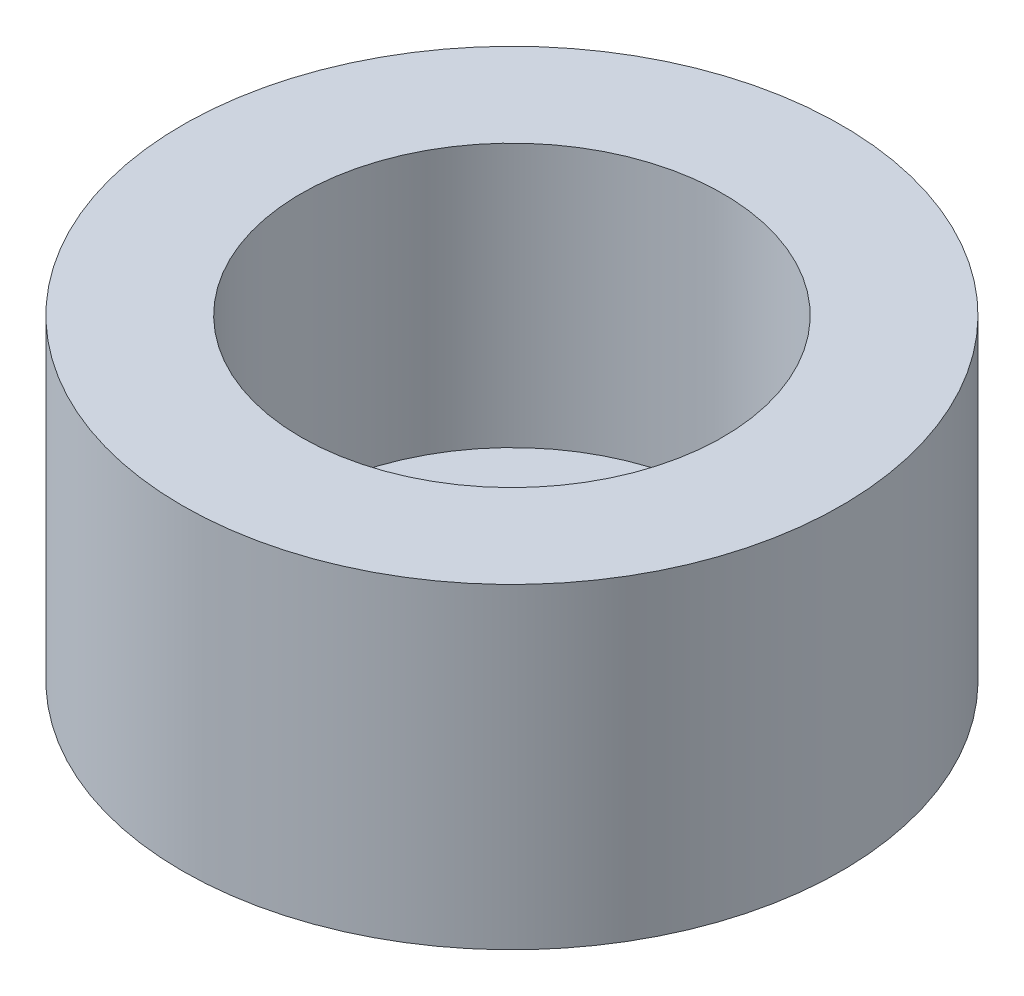
SolidWorks part; units mm, degrees
ref_plane "Front Plane" through (0, 0, 0) normal (0, 0, 1) x (1, 0, 0)
ref_plane "Top Plane" through (0, 0, 0) normal (0, 1, 0) x (1, 0, 0)
ref_plane "Right Plane" through (0, 0, 0) normal (1, 0, 0) x (0, 0, -1)
sketch "Sketch1" plane through (0, 0, 0) normal (0, 1, 0) x (1, 0, 0)
  circle A0 centre (0, 0) radius 12.5
extrude "Boss-Extrude1" add sketch "Sketch1" along normal blind 2
sketch "Sketch2" plane through (0, 2, 0) normal (0, 1, 0) x (1, 0, 0)
  circle A0 centre (0, 0) radius 8
  circle A1 centre (0, 0) radius 12.5
extrude "Boss-Extrude2" add sketch "Sketch2" along normal blind 10
sketch "Sketch3" plane through (0, 2, 0) normal (0, 1, 0) x (1, 0, 0)
  circle A0 centre (0, 0) radius 2.1
extrude "Cut-Extrude1" cut sketch "Sketch3" against normal blind 10
